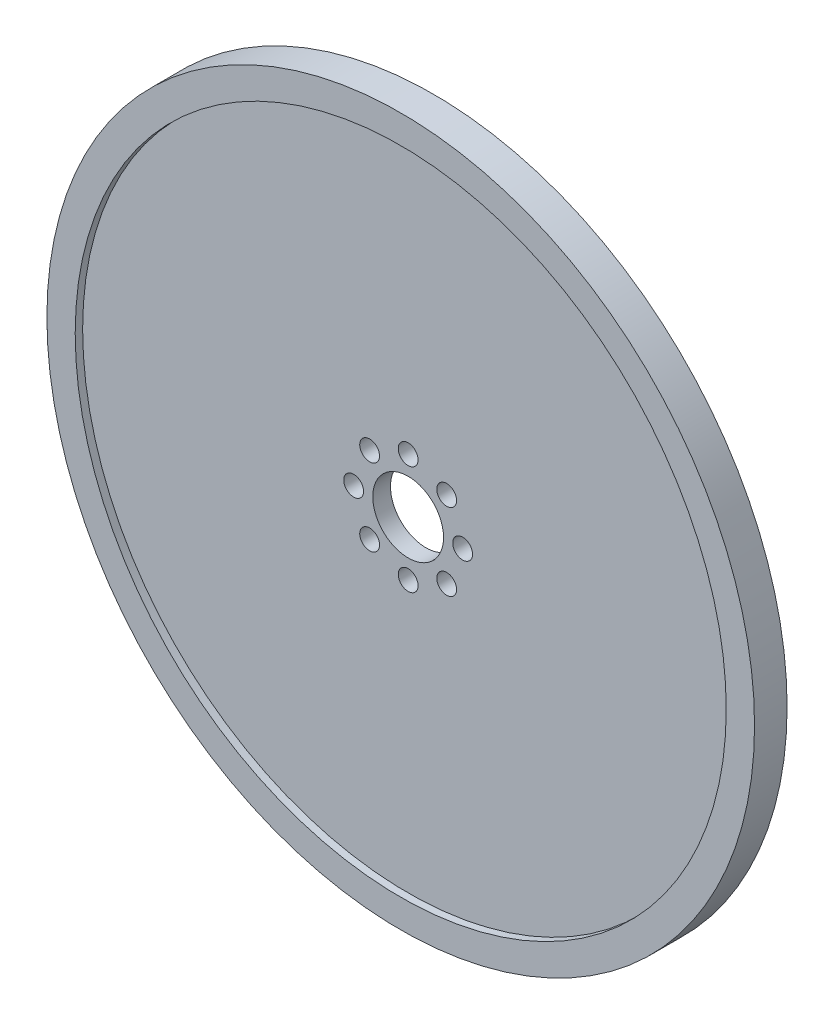
SolidWorks part; units mm, degrees
ref_plane "Front Plane" through (0, 0, 0) normal (0, 0, 1) x (1, 0, 0)
ref_plane "Top Plane" through (0, 0, 0) normal (0, 1, 0) x (1, 0, 0)
ref_plane "Right Plane" through (0, 0, 0) normal (1, 0, 0) x (0, 0, -1)
sketch "Sketch1" plane through (0, 0, 0) normal (0, 0, 1) x (1, 0, 0)
  circle A0 centre (0, 0) radius 63.5
  circle A1 centre (0, 0) radius 58.42
  dimension "D1" = 127
  dimension "D2" = 116.84
extrude "Boss-Extrude1" add sketch "Sketch1" along normal mid plane 5.842
sketch "Sketch3" plane through (0, 0, 0) normal (0, 0, 1) x (1, 0, 0)
  circle A0 centre (0, 0) radius 58.42
  circle A1 centre (0, 0) radius 6.35
  circle A2 centre (0, 9.779) radius 1.778
  circle A3 centre (6.9148, 6.9148) radius 1.778
  circle A4 centre (9.779, 0) radius 1.778
  circle A5 centre (6.9148, -6.9148) radius 1.778
  circle A6 centre (0, -9.779) radius 1.778
  circle A7 centre (-6.9148, -6.9148) radius 1.778
  circle A8 centre (-9.779, 0) radius 1.778
  circle A9 centre (-6.9148, 6.9148) radius 1.778
  dimension "D1" = 12.7
  dimension "D2" = 3.556
  dimension "D5" = 116.84
  dimension "D3" = 9.779
  dimension "D4" = 8
extrude "Boss-Extrude2" add sketch "Sketch3" along normal mid plane 3.175
